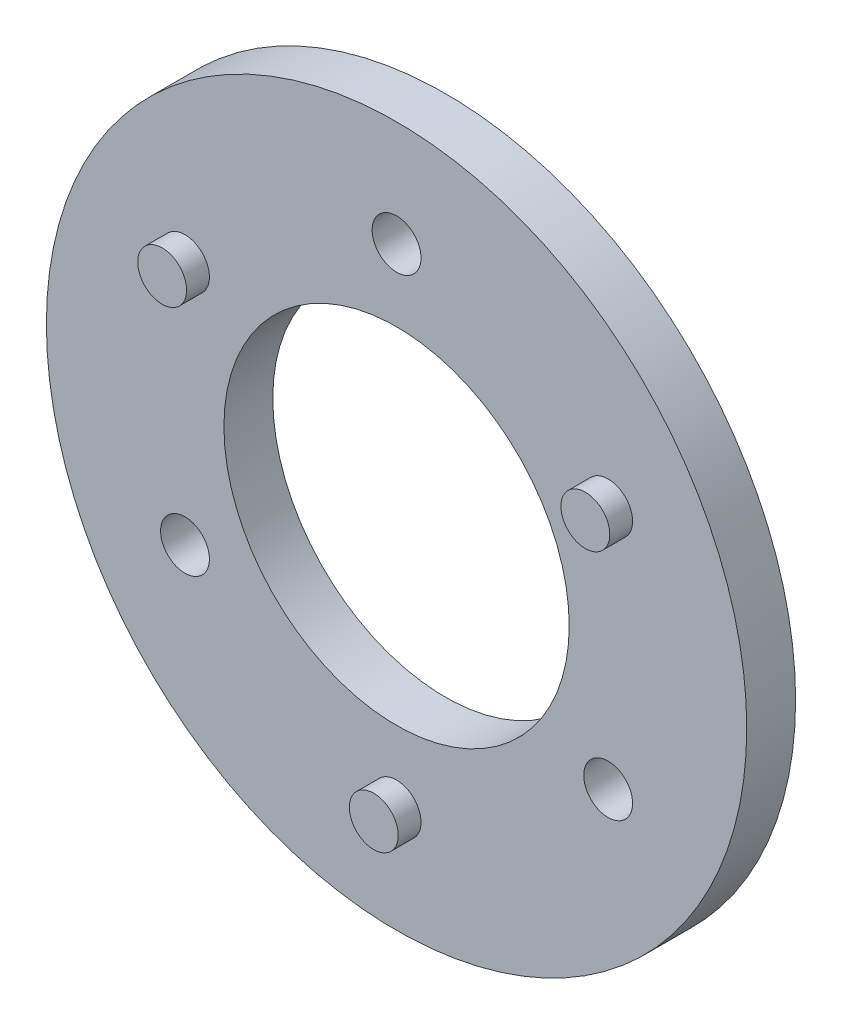
SolidWorks part; units mm, degrees
ref_plane "前基準面" through (0, 0, 0) normal (0, 0, 1) x (1, 0, 0)
ref_plane "上基準面" through (0, 0, 0) normal (0, 1, 0) x (1, 0, 0)
ref_plane "右基準面" through (0, 0, 0) normal (1, 0, 0) x (0, 0, -1)
sketch "草圖1" plane through (0, 0, 0) normal (0, 0, 1) x (1, 0, 0)
  line L0 (0, 0) -> (0, 21.5) construction
  line L1 (0, 0) -> (18.6195, -10.75) construction
  line L2 (0, 0) -> (-18.6195, -10.75) construction
  circle A0 centre (0, 0) radius 21.5
  circle A1 centre (0, 0) radius 10.6
  circle A2 centre (0, 15) radius 1.5
  circle A3 centre (12.9904, -7.5) radius 1.5
  circle A4 centre (-12.9904, -7.5) radius 1.5
  dimension "D1" = 43
  dimension "D2" = 21.2
  dimension "D8" = 3
  dimension "D3" = 120
  dimension "D4" = 120
  dimension "D5" = 15
  dimension "D6" = 15
  dimension "D7" = 15
extrude "填料-伸長1" add sketch "草圖1" along normal blind 3
sketch "草圖2" plane through (0, 0, 3) normal (0, 0, 1) x (1, 0, 0)
  line L0 (0, 0) -> (12.9904, 7.5) construction
  line L1 (0, 0) -> (12.9904, -7.5) construction
  line L2 (0, 0) -> (-12.9904, 7.5) construction
  line L3 (0, 0) -> (0, -15) construction
  circle A0 centre (0, 0) radius 15 construction
  circle A1 centre (12.9904, 7.5) radius 1.5
  circle A2 centre (-12.9904, 7.5) radius 1.5
  circle A3 centre (0, -15) radius 1.5
  dimension "D1" = 30
  dimension "D5" = 3
  dimension "D2" = 60
  dimension "D3" = 120
  dimension "D4" = 120
extrude "填料-伸長2" add sketch "草圖2" along normal blind 1.4
